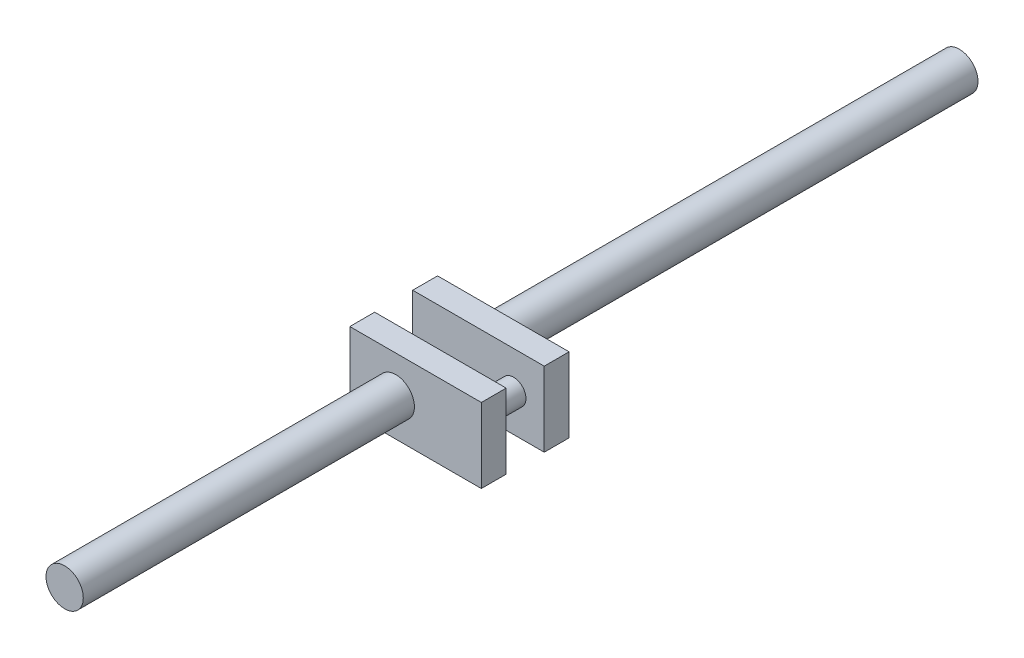
SolidWorks part; units mm, degrees
ref_plane "Front Plane" through (0, 0, 0) normal (0, 0, 1) x (1, 0, 0)
ref_plane "Top Plane" through (0, 0, 0) normal (0, 1, 0) x (1, 0, 0)
ref_plane "Right Plane" through (0, 0, 0) normal (1, 0, 0) x (0, 0, -1)
sketch "Sketch1" plane through (0, 0, 0) normal (0, 0, 1) x (1, 0, 0)
  circle A0 centre (0, 0) radius 7.5
  dimension "D1" = 15
extrude "Boss-Extrude1" add sketch "Sketch1" along normal mid plane 360
sketch "Sketch2" plane through (0, 0, 0) normal (0, 1, 0) x (1, 0, 0)
  line L7 (-90.4563, 140.9615) -> (-300.6998, 140.9615)
  line L8 (-300.6998, -62.6025) -> (-300.6998, 140.9615)
  line L9 (-15.5908, -11.7628) -> (44.4092, -11.7628)
  line L10 (-15.5908, -36.7628) -> (44.4092, -36.7628)
  line L11 (44.4092, -11.7628) -> (44.4092, -36.7628)
  line L12 (-15.5908, -36.7628) -> (-15.5908, -11.7628)
  dimension "D1" = 60
  dimension "D2" = 25
  dimension "D3" = 44.4092
  dimension "D4" = 90.4563
  dimension "D5" = 300.6998
  dimension "D6" = 140.9615
  dimension "D7" = 11.7628
  dimension "D9" = 62.6025
extrude "Cut-Extrude2" cut sketch "Sketch2" against normal mid plane 40 contours L12 L10 L11 L9
sketch "Sketch3" plane through (0, 0, 0) normal (0, 1, 0) x (1, 0, 0)
  line L0 (-18.4915, -11.4578) -> (34.4269, -11.4578)
  line L1 (-18.4915, -36.7628) -> (34.4269, -36.7628)
  point P3 (0, 0)
  point P4 (-18.4915, -36.7628)
  point P9 (0, 0)
  point P10 (0, 0)
  dimension "D1" = 34.4269
  dimension "D2" = 18.4915
  dimension "D3" = 11.4578
extrude "Extrude-Thin1" add sketch "Sketch3" along normal mid plane 30 thin
sketch "Sketch4" plane through (0, 0, 21.4578) normal (0, 0, 1) x (1, 0, 0)
  circle A0 centre (22.0784, 0) radius 5
  dimension "D1" = 10
  dimension "D2" = 22.0784
extrude "Boss-Extrude2" add sketch "Sketch4" along normal blind 25
